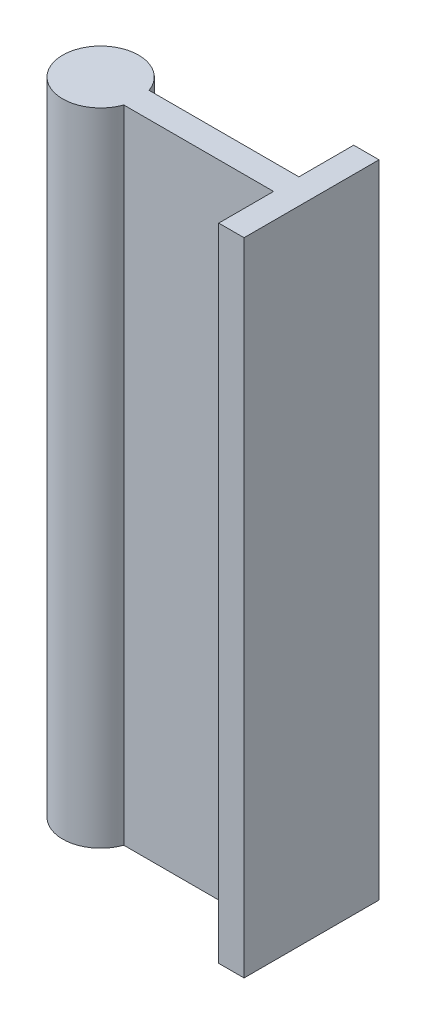
SolidWorks part; units mm, degrees
ref_plane "前基準面" through (0, 0, 0) normal (0, 0, 1) x (1, 0, 0)
ref_plane "上基準面" through (0, 0, 0) normal (0, 1, 0) x (1, 0, 0)
ref_plane "右基準面" through (0, 0, 0) normal (1, 0, 0) x (0, 0, -1)
sketch "草圖1" plane through (0, 0, 0) normal (0, 1, 0) x (1, 0, 0)
  circle A0 centre (0, 0) radius 2.25
  dimension "D1" = 4.5
extrude "填料-伸長1" add sketch "草圖1" along normal blind 38
ref_plane "平面1" through (3, 0, 0) normal (1, 0, 0) x (0, 0, -1)
sketch "草圖2" plane through (3, 0, 0) normal (1, 0, 0) x (0, 0, -1)
  line L0 (0, -962) -> (0, 49038) construction
  line L1 (2.25, 38) -> (-2.25, 38) construction
  line L2 (-2.25, 0) -> (2.25, 0) construction
  line L3 (-0.75, 38) -> (0.75, 38)
  line L4 (-0.75, 38) -> (-0.75, 0)
  line L5 (-0.75, 0) -> (0.75, 0)
  line L6 (0.75, 38) -> (0.75, 0)
  line L7 (-0.75, 38) -> (0.75, 0) construction
  line L8 (-0.75, 0) -> (0.75, 38) construction
  point P1 (0, 19)
  point P5 (0, 38)
  dimension "D1" = 0
  dimension "D2" = 1.5
  dimension "D3" = 0
extrude "填料-伸長2" add sketch "草圖2" along normal blind 8 and the other way blind 3
sketch "草圖3" plane through (11, 0, 0) normal (1, 0, 0) x (0, 0, -1)
  line L0 (0, -962) -> (0, 49038) construction
  line L1 (0.75, 38) -> (-0.75, 38) construction
  line L2 (-2.25, 0) -> (2.25, 0) construction
  line L3 (-4, 38) -> (4, 38)
  line L4 (-4, 38) -> (-4, 0)
  line L5 (-4, 0) -> (4, 0)
  line L6 (4, 38) -> (4, 0)
  line L7 (-4, 38) -> (4, 0) construction
  line L8 (-4, 0) -> (4, 38) construction
  point P1 (0, 19)
  point P5 (0, 38)
  dimension "D1" = 0
  dimension "D2" = 0
  dimension "D3" = 8
extrude "填料-伸長3" add sketch "草圖3" along normal blind 1.5
